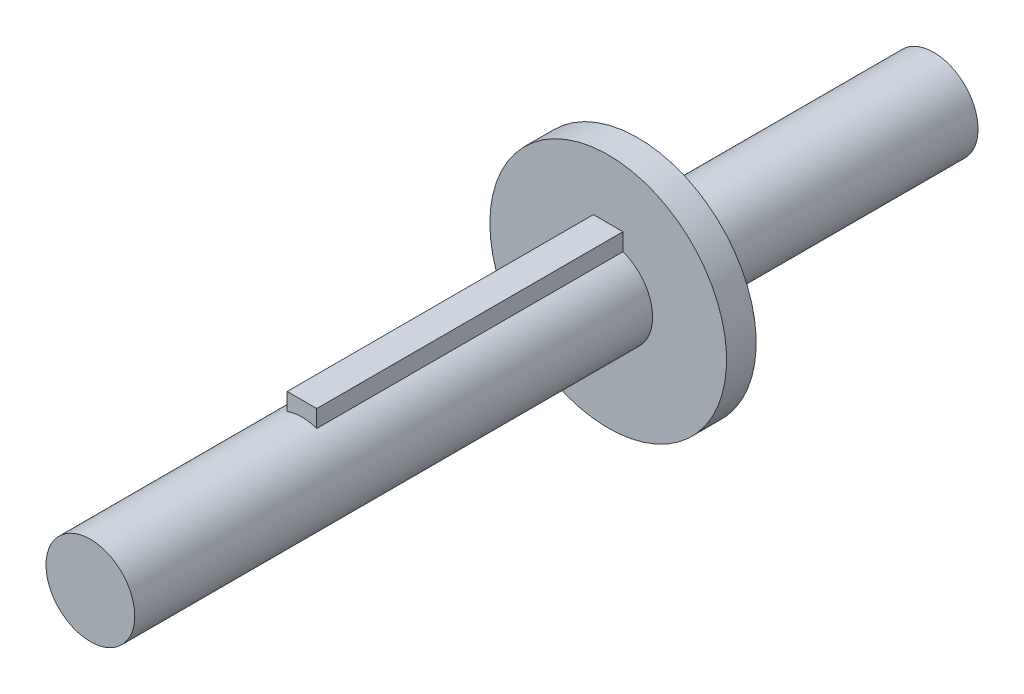
SolidWorks part; units mm, degrees
ref_plane "Front Plane" through (0, 0, 0) normal (0, 0, 1) x (1, 0, 0)
ref_plane "Top Plane" through (0, 0, 0) normal (0, 1, 0) x (1, 0, 0)
ref_plane "Right Plane" through (0, 0, 0) normal (1, 0, 0) x (0, 0, -1)
sketch "Sketch1" plane through (0, 0, 0) normal (0, 0, 1) x (1, 0, 0)
  circle A0 centre (0, 0) radius 3
  dimension "D1" = 6
extrude "Boss-Extrude1" add sketch "Sketch1" along normal blind 35
sketch "Sketch2" plane through (0, 0, 0) normal (0, 0, -1) x (-1, 0, 0)
  line L0 (-1, 2.8284) -> (-1, 3.9984)
  line L1 (-1, 3.9984) -> (1, 3.9984)
  line L2 (1, 3.9984) -> (1, 2.8284)
  line L3 (-1, 2.8284) -> (1, 2.8284)
  circle A0 centre (0, 0) radius 3 construction
  point P4 (0, 3.9984)
  dimension "D1" = 1.17
  dimension "D2" = 2
sketch "Sketch3" plane through (0, 0, 0) normal (0, 0, -1) x (-1, 0, 0)
  circle A0 centre (0, 0) radius 8
extrude "Boss-Extrude3" add sketch "Sketch3" along normal blind 2
extrude "Boss-Extrude4" add sketch "Sketch2" against normal blind 20.7
sketch "Sketch4" plane through (0, 0, -2) normal (0, 0, -1) x (-1, 0, 0)
  circle A0 centre (0, 0) radius 3
  dimension "D1" = 6
extrude "Boss-Extrude5" add sketch "Sketch4" along normal blind 20
